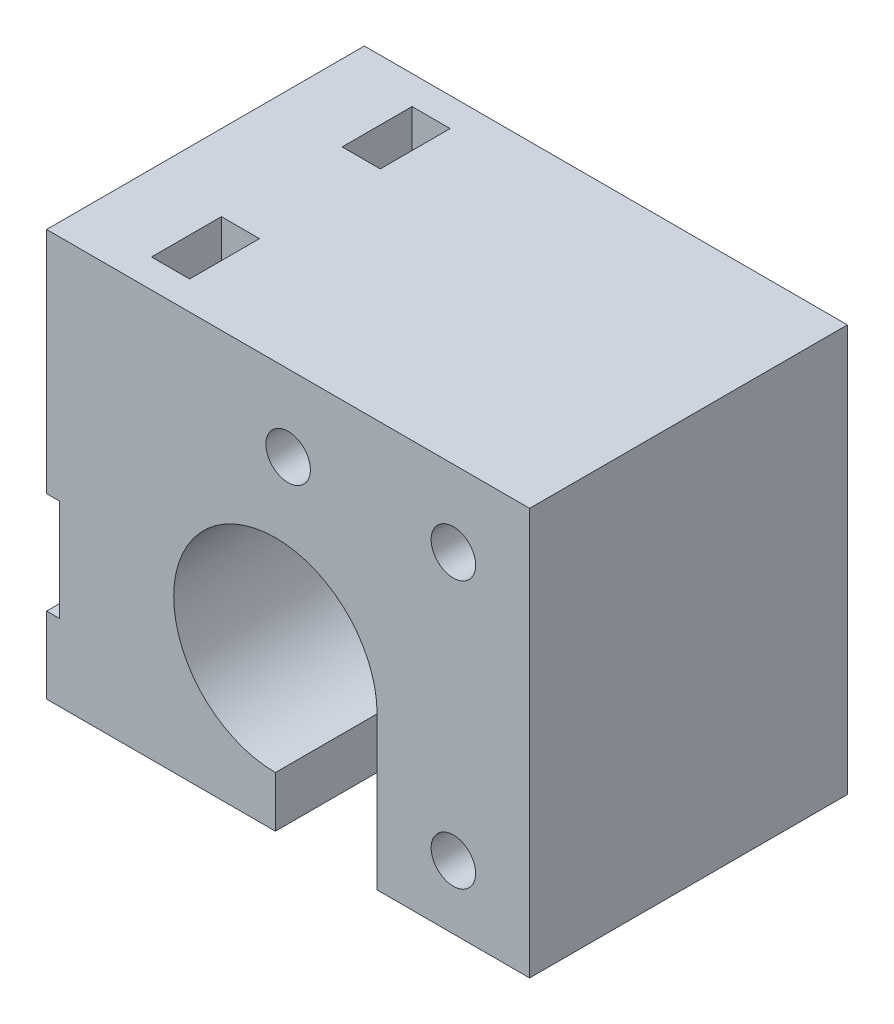
SolidWorks part; units mm, degrees
ref_plane "Спереди" through (0, 0, 0) normal (0, 0, 1) x (1, 0, 0)
ref_plane "Сверху" through (0, 0, 0) normal (0, 1, 0) x (1, 0, 0)
ref_plane "Справа" through (0, 0, 0) normal (1, 0, 0) x (0, 0, -1)
sketch "Эскиз2" plane through (0, 0, 0) normal (0, 0, 1) x (1, 0, 0)
  line L0 (8, 0) -> (8, -12)
  line L1 (8, -12) -> (20, -12)
  line L2 (0, -12) -> (0, -8)
  line L3 (20, -12) -> (20, 20)
  line L4 (20, 20) -> (-18, 20)
  line L5 (-18, 20) -> (-18, -12)
  line L6 (-18, -12) -> (0, -12)
  line L7 (14, -12) -> (14, 20) construction
  line L9 (20, 14) -> (-18, 14) construction
  arc A0 (8, 0) -> (0, -8) centre (0, 0) ccw
  circle A1 centre (1, 14) radius 1.75
  circle A2 centre (14, -7) radius 1.75
  circle A3 centre (14, 14) radius 1.75
  point P11 (0, -10)
  dimension "D1" = 8
  dimension "D8" = 5
  dimension "D9" = 3.5
  dimension "D2" = 12
  dimension "D3" = 12
  dimension "D4" = 8
  dimension "D5" = 32
  dimension "D6" = 18
  dimension "D7" = 6
extrude "Бобышка-Вытянуть1" add sketch "Эскиз2" along normal blind 25
sketch "Эскиз3" plane through (-18, 0, 0) normal (-1, 0, 0) x (0, 0, 1)
  line L0 (0, 20) -> (0, -12) construction
  line L1 (0, 2) -> (1, 2)
  line L2 (0, 2) -> (0, -6)
  line L3 (0, -6) -> (1, -6)
  line L4 (1, 2) -> (1, -6)
  line L5 (25, -12) -> (0, -12) construction
  line L6 (3, 2) -> (3, -6)
  line L7 (2, 2) -> (2, -6)
  line L8 (2, -6) -> (3, -6)
  line L9 (2, 2) -> (3, 2)
  line L10 (5, 2) -> (5, -6)
  line L11 (4, 2) -> (4, -6)
  line L12 (4, -6) -> (5, -6)
  line L13 (4, 2) -> (5, 2)
  line L14 (7, 2) -> (7, -6)
  line L15 (6, 2) -> (6, -6)
  line L16 (6, -6) -> (7, -6)
  line L17 (6, 2) -> (7, 2)
  line L18 (9, 2) -> (9, -6)
  line L19 (8, 2) -> (8, -6)
  line L20 (8, -6) -> (9, -6)
  line L21 (8, 2) -> (9, 2)
  line L22 (11, 2) -> (11, -6)
  line L23 (10, 2) -> (10, -6)
  line L24 (10, -6) -> (11, -6)
  line L25 (10, 2) -> (11, 2)
  line L26 (13, 2) -> (13, -6)
  line L27 (12, 2) -> (12, -6)
  line L28 (12, -6) -> (13, -6)
  line L29 (12, 2) -> (13, 2)
  line L30 (15, 2) -> (15, -6)
  line L31 (14, 2) -> (14, -6)
  line L32 (14, -6) -> (15, -6)
  line L33 (14, 2) -> (15, 2)
  line L34 (17, 2) -> (17, -6)
  line L35 (16, 2) -> (16, -6)
  line L36 (16, -6) -> (17, -6)
  line L37 (16, 2) -> (17, 2)
  line L38 (19, 2) -> (19, -6)
  line L39 (18, 2) -> (18, -6)
  line L40 (18, -6) -> (19, -6)
  line L41 (18, 2) -> (19, 2)
  line L42 (21, 2) -> (21, -6)
  line L43 (20, 2) -> (20, -6)
  line L44 (20, -6) -> (21, -6)
  line L45 (20, 2) -> (21, 2)
  line L46 (23, 2) -> (23, -6)
  line L47 (22, 2) -> (22, -6)
  line L48 (22, -6) -> (23, -6)
  line L49 (22, 2) -> (23, 2)
  line L50 (25, 2) -> (25, -6)
  line L51 (24, 2) -> (24, -6)
  line L52 (24, -6) -> (25, -6)
  line L53 (24, 2) -> (25, 2)
  dimension "D1" = 8
  dimension "D2" = 6
  dimension "D3" = 1
  dimension "D4" = 13
extrude "Вырез-Вытянуть1" cut sketch "Эскиз3" against normal blind 1
sketch "Эскиз4" plane through (-18, 0, 0) normal (-1, 0, 0) x (0, 0, 1)
  line L0 (0, 5) -> (25, 5) construction
  line L1 (0, 20) -> (0, 2) construction
  line L2 (25, 20) -> (25, 2) construction
  line L4 (0, -6) -> (0, -12) construction
  line L5 (0, -9) -> (25, -9) construction
  line L6 (25, -6) -> (25, -12) construction
  line L7 (25, -12) -> (0, -12) construction
  line L8 (5, -9) -> (5, 5) construction
  line L10 (20, -9) -> (20, 5) construction
  circle A0 centre (5, 5) radius 2
  circle A1 centre (20, 5) radius 2
  circle A2 centre (20, -9) radius 2
  circle A3 centre (5, -9) radius 2
  dimension "D5" = 4
  dimension "D1" = 14
  dimension "D2" = 3
  dimension "D3" = 5
  dimension "D4" = 5
extrude "Вырез-Вытянуть2" cut sketch "Эскиз4" against normal blind 9
sketch "Эскиз5" plane through (0, -12, 0) normal (0, -1, 0) x (1, 0, 0)
  line L0 (-9, 5) -> (-12, 5) construction
  line L1 (-9, 2.25) -> (-12, 2.25)
  line L2 (-9, 2.25) -> (-9, 7.75)
  line L3 (-9, 7.75) -> (-12, 7.75)
  line L4 (-12, 2.25) -> (-12, 7.75)
  line L5 (-9, 17.25) -> (-12, 17.25)
  line L6 (-9, 17.25) -> (-9, 22.75)
  line L7 (-9, 22.75) -> (-12, 22.75)
  line L8 (-12, 17.25) -> (-12, 22.75)
  line L9 (-18, 25) -> (-18, 0) construction
  line L10 (-9, 20) -> (-12, 20) construction
  line L12 (-18, 0) -> (0, 0) construction
  line L13 (-18, 25) -> (0, 25) construction
  dimension "D1" = 3
  dimension "D2" = 3
  dimension "D3" = 5.5
  dimension "D4" = 9
  dimension "D5" = 5
  dimension "D6" = 5
extrude "Вырез-Вытянуть3" cut sketch "Эскиз5" against normal through all
